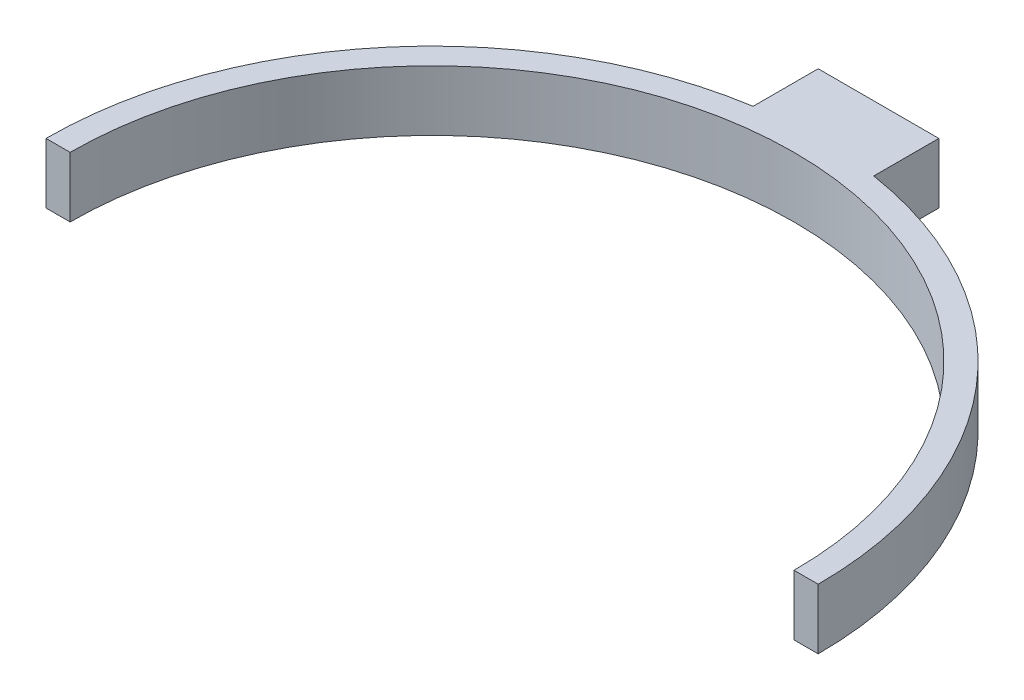
SolidWorks part; units mm, degrees
ref_plane "前视基准面" through (0, 0, 0) normal (0, 0, 1) x (1, 0, 0)
ref_plane "上视基准面" through (0, 0, 0) normal (0, 1, 0) x (1, 0, 0)
ref_plane "右视基准面" through (0, 0, 0) normal (1, 0, 0) x (0, 0, -1)
sketch "草图1" plane through (0, 0, 0) normal (0, 1, 0) x (1, 0, 0)
  line L0 (-32, 0) -> (-30, 0)
  line L1 (30, 0) -> (32, 0)
  arc A0 (30, 0) -> (-30, 0) centre (0, 0) ccw
  arc A1 (32, 0) -> (-32, 0) centre (0, 0) ccw
extrude "凸台-拉伸1" add sketch "草图1" along normal blind 5
sketch "草图2" plane through (0, 0, 0) normal (0, 1, 0) x (1, 0, 0)
  line L0 (0, 32) -> (0, 37)
  line L1 (0, 37) -> (5, 37)
  line L2 (5, 37) -> (5, 30.4653)
  line L3 (5, 30.4653) -> (-5, 30.4653)
  line L4 (-5, 30.4653) -> (-5, 37)
  line L5 (-5, 37) -> (0, 37)
  arc A0 (32, 0) -> (-32, 0) centre (0, 0) ccw construction
extrude "凸台-拉伸2" add sketch "草图2" along normal blind 5
